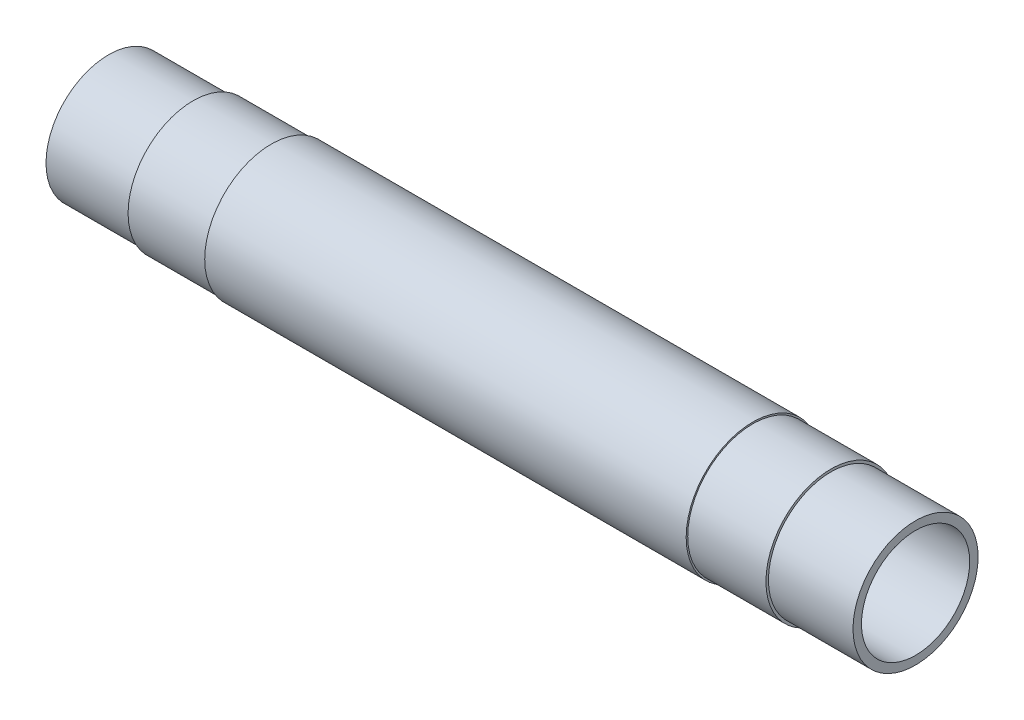
SolidWorks part; units mm, degrees
material "AISI 1020"
ref_plane "Спереди" through (0, 0, 0) normal (0, 0, 1) x (1, 0, 0)
ref_plane "Сверху" through (0, 0, 0) normal (0, 1, 0) x (1, 0, 0)
ref_plane "Справа" through (0, 0, 0) normal (1, 0, 0) x (0, 0, -1)
sketch "Эскиз1" plane through (0, 0, 0) normal (1, 0, 0) x (0, 0, -1)
  circle B0 centre (0, 0) radius 8.65
  circle B1 centre (0, 0) radius 10.65
sketch_block_instance "Труба 21_3х2-1"
sketch_block "Труба 21_3х2" parameters "D2"=21.3, "D1"=2
extrude "Бобышка-Вытянуть1" add sketch "Эскиз1" against normal up to surface (64.5 mm away)
sketch "Эскиз2" plane through (0, 0, 0) normal (0, 0, 1) x (1, 0, 0)
  line L0 (-38.4802, 10.65) -> (-64.5, 10.65)
  line L1 (0, 10.65) -> (-64.5, 10.65) construction
  line L2 (-64.5, 10.65) -> (-64.5, 10)
  line L3 (-64.5, -63.5) -> (-64.5, 63.5) construction
  line L4 (-64.5, 10) -> (-50.9802, 10)
  line L5 (-50.9802, 10) -> (-50.9802, 10.4)
  line L6 (-50.9802, 10.4) -> (-38.4802, 10.4)
  line L7 (-38.4802, 10.4) -> (-38.4802, 10.65)
  line L8 (-52, 10) -> (-63, 10) construction
  line L9 (-1000, 0) -> (49000, 0) construction
  arc A0 (-52, 10) -> (-50.5, 11.5) centre (-52, 11.5) ccw construction
  dimension "D1" = 20.8
  dimension "D2" = 12.5
revolve "Вырез-Повернуть1" cut sketch "Эскиз2" angle 360 about L9
mirror "Зеркальное отражение1" about plane through (0, 0, 0) normal (1, 0, 0) of bodies 104
